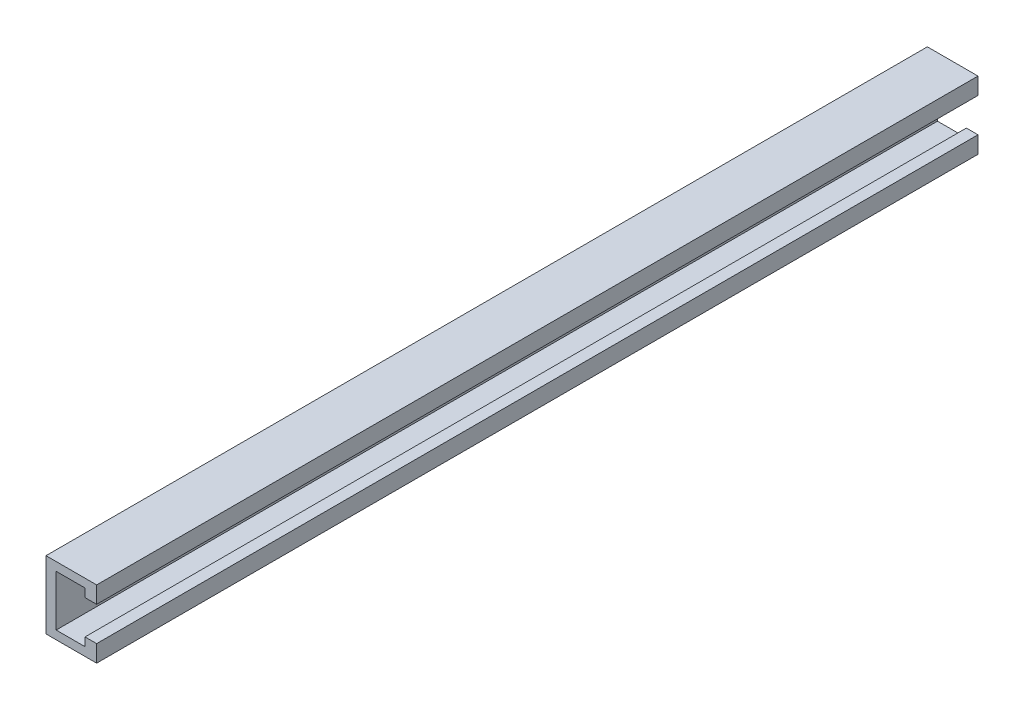
SolidWorks part; units mm, degrees
ref_plane "Front Plane" through (0, 0, 0) normal (0, 0, 1) x (1, 0, 0)
ref_plane "Top Plane" through (0, 0, 0) normal (0, 1, 0) x (1, 0, 0)
ref_plane "Right Plane" through (0, 0, 0) normal (1, 0, 0) x (0, 0, -1)
sketch "Sketch1" plane through (0, 0, 0) normal (0, 0, 1) x (1, 0, 0)
  line L0 (13.996, 10.4913) -> (22.7046, 10.4913)
  line L1 (-15.2399, 23.0933) -> (22.7046, 23.0933)
  line L2 (-15.2399, 23.0933) -> (-15.2399, -27.7067)
  line L3 (-15.2399, -27.7067) -> (22.7046, -27.7067)
  line L4 (22.7046, 23.0933) -> (22.7046, 10.4913)
  line L5 (-7.6199, 16.7433) -> (13.996, 16.7433)
  line L6 (-7.6199, 16.7433) -> (-7.6199, -21.3567)
  line L7 (-7.6199, -21.3567) -> (13.996, -21.3567)
  line L8 (13.996, 16.7433) -> (13.996, 10.4913)
  line L9 (13.996, -15.0067) -> (22.7046, -15.0067)
  line L10 (13.996, -15.0067) -> (13.996, -21.3567)
  line L11 (22.7046, -15.0067) -> (22.7046, -27.7067)
  dimension "D1" = 50.8
  dimension "D2" = 38.1
  dimension "D3" = 6.35
  dimension "D4" = 7.62
  dimension "D5" = 12.602
  dimension "D6" = 12.7
extrude "Boss-Extrude1" add sketch "Sketch1" along normal blind 660.4
sketch "Sketch2" plane through (-15.2399, 0, 0) normal (-1, 0, 0) x (0, 0, 1)
  line L0 (660.4, 23.0933) -> (0, 23.0933) construction
  line L1 (0, 23.0933) -> (0, -27.7067) construction
  circle A0 centre (25.4, -2.3067) radius 6.35
  circle A1 centre (279.4, -2.3067) radius 6.35
  dimension "D1" = 25.4
  dimension "D4" = 254
  dimension "D2" = 25.4
  dimension "D3" = 2
extrude "Cut-Extrude1" cut sketch "Sketch2" against normal through all
